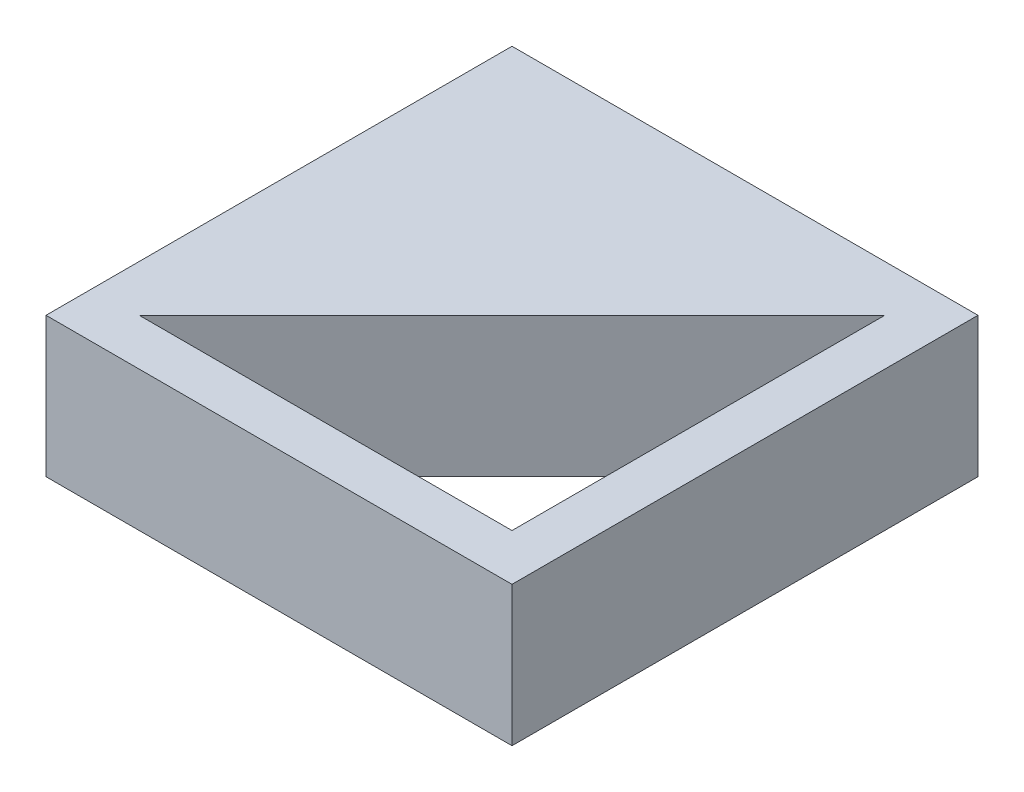
SolidWorks part; units mm, degrees
ref_plane "Front Plane" through (0, 0, 0) normal (0, 0, 1) x (1, 0, 0)
ref_plane "Top Plane" through (0, 0, 0) normal (0, 1, 0) x (1, 0, 0)
ref_plane "Right Plane" through (0, 0, 0) normal (1, 0, 0) x (0, 0, -1)
sketch "Sketch1" plane through (0, 0, 0) normal (0, 1, 0) x (1, 0, 0)
  line L1 (50, 50) -> (-50, 50)
  line L2 (50, 50) -> (50, -50)
  line L3 (50, -50) -> (-50, -50)
  line L4 (-50, 50) -> (-50, -50)
  line L5 (50, 50) -> (-50, -50) construction
  line L6 (50, -50) -> (-50, 50) construction
  point P0 (0, 0)
  dimension "D1" = 100
extrude "Boss-Extrude1" add sketch "Sketch1" along normal blind 30
sketch "Sketch2" plane through (0, 30, 0) normal (0, 1, 0) x (1, 0, 0)
  line L0 (40, 40) -> (40, -40)
  line L1 (40, -40) -> (-40, -40)
  line L2 (-40, -40) -> (40, 40)
  line L3 (50, -50) -> (50, 50) construction
  line L4 (-50, -50) -> (50, -50) construction
  dimension "D1" = 10
  dimension "D2" = 10
extrude "Cut-Extrude1" cut sketch "Sketch2" against normal through all
